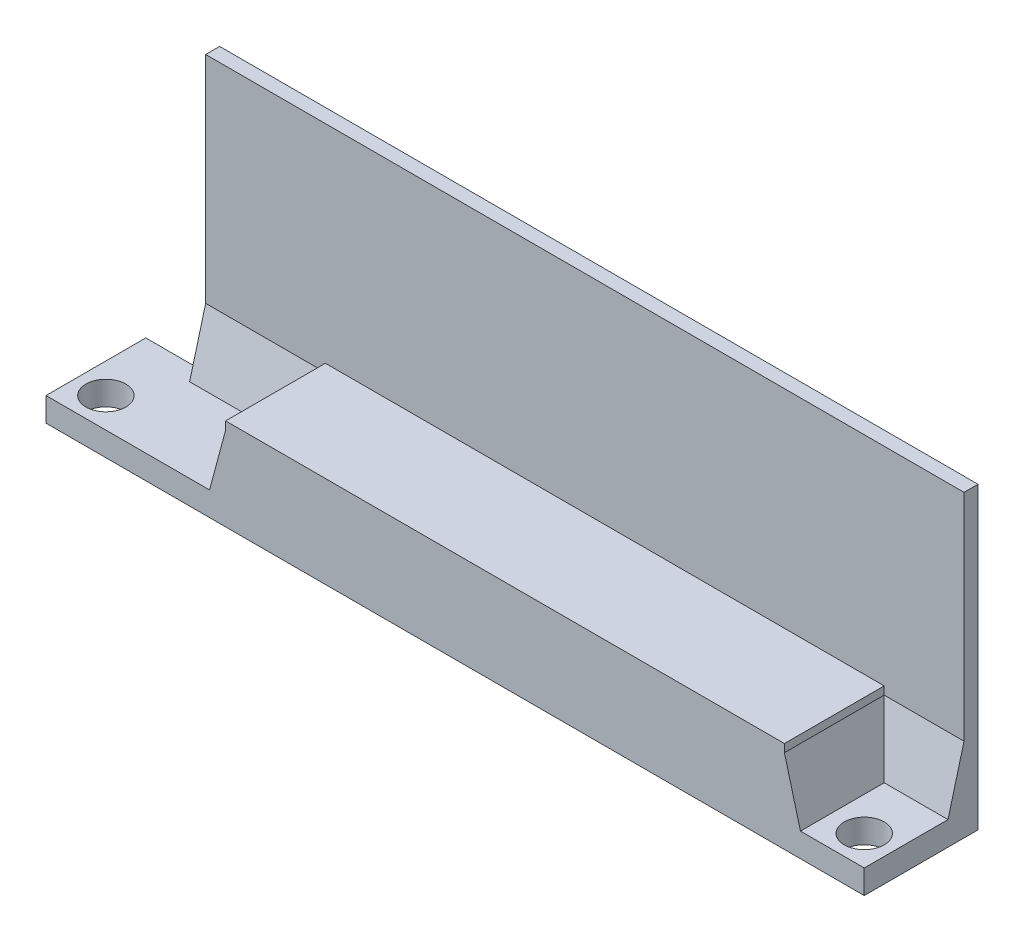
SolidWorks part; units mm, degrees
ref_plane "Front Plane" through (0, 0, 0) normal (0, 0, 1) x (1, 0, 0)
ref_plane "Top Plane" through (0, 0, 0) normal (0, 1, 0) x (1, 0, 0)
ref_plane "Right Plane" through (0, 0, 0) normal (1, 0, 0) x (0, 0, -1)
sketch "Sketch1" plane through (0, 0, 0) normal (0, 1, 0) x (1, 0, 0)
  line L0 (20.5, 5) -> (20.5, 0) construction
  line L1 (0, 0) -> (41, 0)
  line L2 (0, 0) -> (0, 5)
  line L3 (0, 5) -> (41, 5)
  line L4 (41, 0) -> (41, 5)
  line L5 (0, 0) -> (41, 5) construction
  line L6 (0, 5) -> (41, 0) construction
  circle A0 centre (1.5, 1.5) radius 1
  circle A1 centre (39.5, 1.5) radius 1
  point P4 (20.5, 2.5)
  dimension "D1" = 2
  dimension "D2" = 41
  dimension "D3" = 38
  dimension "D4" = 1.5
  dimension "D5" = 5
extrude "Boss-Extrude1" add sketch "Sketch1" along normal blind 10
sketch "Sketch2" plane through (0, 0, 0) normal (0, 0, 1) x (1, 0, 0)
  line L0 (0, 1.2) -> (41, 1.2)
  line L1 (0, 10) -> (0, 0) construction
  line L2 (41, 10) -> (41, 0) construction
  line L5 (9, 1.2) -> (37, 1.2)
  line L7 (9, 1.2) -> (9, 4.6)
  line L8 (9, 4.6) -> (37, 4.6)
  line L9 (0, 1.2) -> (0, 0)
  line L10 (0, 0) -> (41, 0)
  line L11 (41, 1.2) -> (41, -0.1138)
  line L12 (37, 1.2) -> (37, 4.6)
  line L13 (9, 1.2) -> (37, 4.6) construction
  line L14 (9, 4.6) -> (37, 1.2) construction
  point P10 (23, 2.9)
  line M8 (41, 0) -> (41, 10)
  line M9 (41, 10) -> (0, 10)
  line M10 (0, 10) -> (0, 0)
  dimension "D1" = 1.2
  dimension "D2" = 28
  dimension "D3" = 4
  dimension "D4" = 4.6
extrude "Cut-Extrude1" cut sketch "Sketch2" against normal blind 10 contours L12 L0 L7 L8 M8 M9 M10
sketch "Sketch4" plane through (0, 0, -5) normal (0, 0, -1) x (-1, 0, 0)
  line L0 (0, 0) -> (-41, 0) construction
  line L1 (-41, 15) -> (-3, 15)
  line L2 (-41, 15) -> (-41, 0)
  line L3 (-41, 0) -> (-3, 0)
  line L4 (-3, 15) -> (-3, 0)
  line L5 (-41, 15) -> (-3, 0) construction
  line L6 (-41, 0) -> (-3, 15) construction
  line L7 (-41, 1.2) -> (-41, 0) construction
  point P4 (-22, 7.5)
  dimension "D1" = 38
  dimension "D2" = 15
extrude "Boss-Extrude2" add sketch "Sketch4" along normal blind 0.7
sketch "Sketch3" plane through (0, 0, 0) normal (0, 0, 1) x (1, 0, 0)
  line L0 (0, 0) -> (41, 0) construction
  line L1 (9.8, 0) -> (36.2, 0)
  line L2 (9.8, 0) -> (9.8, 3.8)
  line L3 (9.8, 3.8) -> (36.2, 3.8)
  line L4 (36.2, 0) -> (36.2, 3.8)
  line L5 (9.8, 0) -> (36.2, 3.8) construction
  line L6 (9.8, 3.8) -> (36.2, 0) construction
  line L7 (9, 1.2) -> (9, 4.6) construction
  line L8 (37, 1.2) -> (37, 4.6) construction
  line L9 (9, 4.6) -> (37, 4.6) construction
  point P4 (23, 1.9)
  point P9 (9, 2.9)
  dimension "D1" = 0.8
  dimension "D2" = 0.8
  dimension "D3" = 0.8
extrude "Cut-Extrude2" cut sketch "Sketch3" against normal blind 10
chamfer "Chamfer1" distance 3 angle 15 4 edges at (37, 1.2, -2.5) (9, 1.2, -2.5) (39, 1.2, -5) (6, 1.2, -5)
sketch "Sketch7" plane through (0, 0, 0) normal (0, 0, 1) x (1, 0, 0)
  line L1 (9.8, 3.8) -> (36.2, 3.8)
  line L2 (9.8, 3.8) -> (9.8, 0)
  line L3 (9.8, 0) -> (36.2, 0)
  line L4 (36.2, 3.8) -> (36.2, 0)
  line L5 (9.8, 3.8) -> (36.2, 0) construction
  line L6 (9.8, 0) -> (36.2, 3.8) construction
  point P4 (23, 1.9)
extrude "Boss-Extrude3" add sketch "Sketch7" against normal blind 0.8
